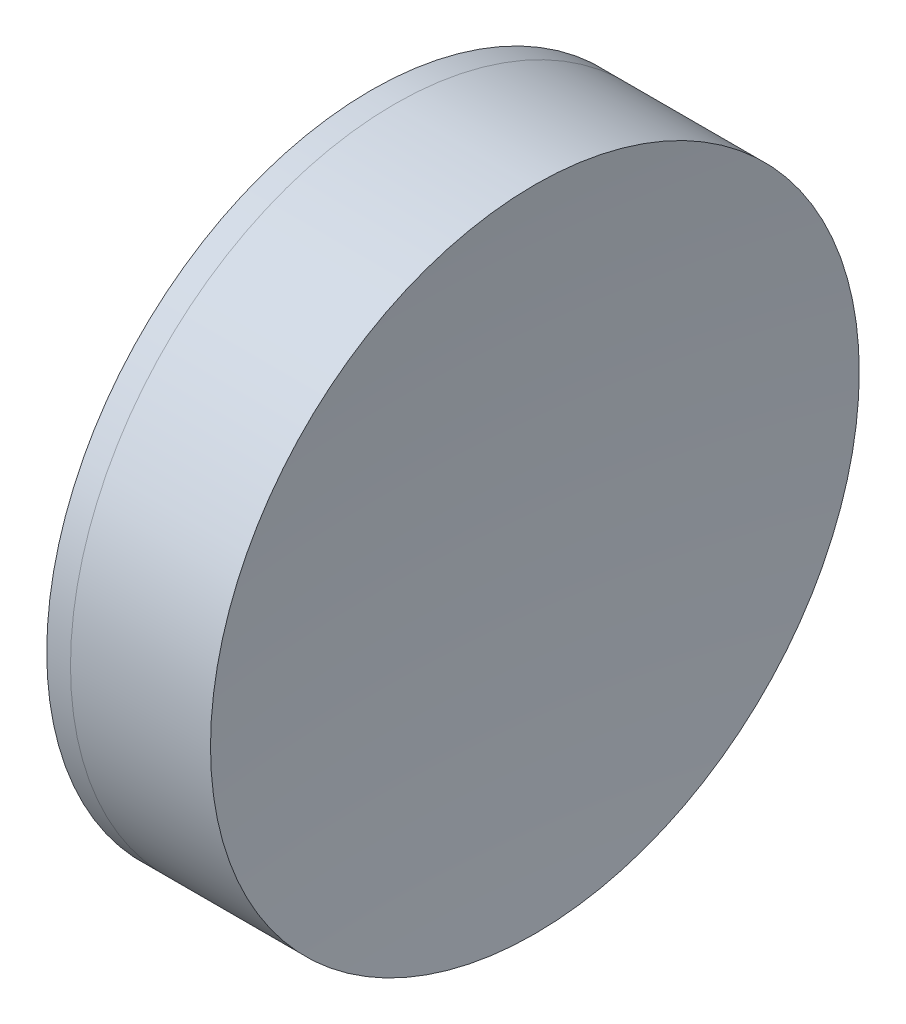
SolidWorks part; units mm, degrees
ref_plane "前视基准面" through (0, 0, 0) normal (0, 0, 1) x (1, 0, 0)
ref_plane "上视基准面" through (0, 0, 0) normal (0, 1, 0) x (1, 0, 0)
ref_plane "右视基准面" through (0, 0, 0) normal (1, 0, 0) x (0, 0, -1)
sketch "草图1" plane through (0, 0, 0) normal (0, 1, 0) x (1, 0, 0)
  line L0 (-0.8161, 0) -> (118.0272, 0) construction
  line L1 (101.8246, -25.4) -> (103.6841, -25.4)
  line L2 (101.8246, 25.4) -> (103.6841, 25.4)
  arc A0 (103.6841, -25.4) -> (103.6841, 25.4) centre (62.5903, 0) ccw
  arc A1 (101.8246, 25.4) -> (101.8246, -25.4) centre (138.5703, 0) ccw
  point P10 (93.9003, 0)
  point P11 (110.9003, 0)
  dimension "D3" = 44.67
  dimension "D4" = 48.31
  dimension "D1" = 25.4
  dimension "D2" = 25.4
  dimension "D5" = 17
revolve "旋转1" add sketch "草图1" angle 360 about L0
sketch "草图2" plane through (0, 0, 0) normal (0, 1, 0) x (1, 0, 0)
  line L0 (-0.5519, 0) -> (162.8134, 0) construction
  line L2 (103.6841, 25.4) -> (114.6469, 25.4)
  line L3 (103.6841, -25.4) -> (114.6469, -25.4)
  arc A0 (114.6469, 25.4) -> (114.6469, -25.4) centre (372.8003, 0) ccw
  arc A1 (103.6841, -25.4) -> (103.6841, 25.4) centre (62.5903, 0) ccw construction
  arc A2 (103.6841, -25.4) -> (103.6841, 25.4) centre (62.5903, 0) ccw
  point P4 (110.9003, 0)
  point P8 (113.4003, 0)
  dimension "D1" = 259.4
  dimension "D2" = 2.5
revolve "旋转2" add sketch "草图2" angle 360 about L0
